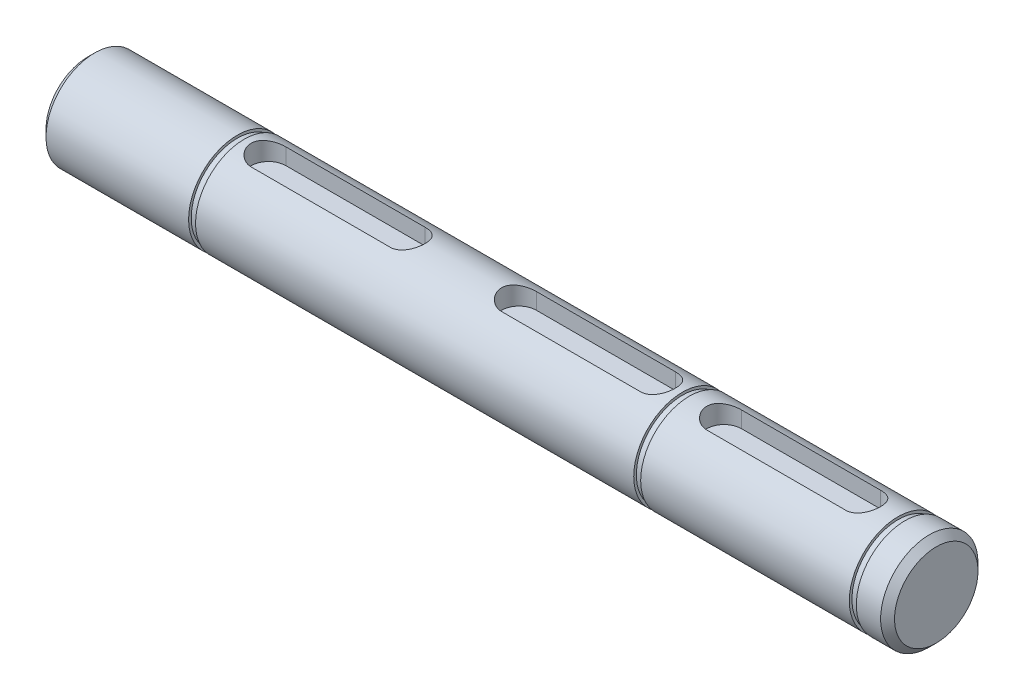
SolidWorks part; units mm, degrees
ref_plane "Front Plane" through (0, 0, 0) normal (0, 0, 1) x (1, 0, 0)
ref_plane "Top Plane" through (0, 0, 0) normal (0, 1, 0) x (1, 0, 0)
ref_plane "Right Plane" through (0, 0, 0) normal (1, 0, 0) x (0, 0, -1)
sketch "Sketch1" plane through (0, 0, 0) normal (1, 0, 0) x (0, 0, -1)
  circle A0 centre (0, 0) radius 7
  dimension "D1" = 14
extrude "Boss-Extrude1" add sketch "Sketch1" along normal mid plane 68
ref_plane "Plane1" through (0, 7, 0) normal (0, 1, 0) x (1, 0, 0)
sketch "Sketch4" plane through (0, 7, 0) normal (0, 1, 0) x (1, 0, 0)
  line L0 (-28, 0) -> (-8, 0) construction
  line L1 (-28, 2.5) -> (-8, 2.5)
  line L2 (-28, -2.5) -> (-8, -2.5)
  arc A0 (-28, 2.5) -> (-28, -2.5) centre (-28, 0) ccw
  arc A1 (-8, -2.5) -> (-8, 2.5) centre (-8, 0) ccw
  point P3 (-18, 0)
  dimension "D2" = 2.5
  dimension "D1" = 20
  dimension "D3" = 8
extrude "Cut-Extrude1" cut sketch "Sketch4" against normal blind 2.8
mirror "Mirror1" about plane through (0, 0, 0) normal (1, 0, 0) of "Cut-Extrude1"
sketch "Sketch5" plane through (-34, 0, 0) normal (-1, 0, 0) x (0, 0, 1)
  circle A1 centre (0, 0) radius 7
  circle A2 centre (0, 0) radius 7
  dimension "D1" = 0
extrude "Boss-Extrude3" add sketch "Sketch5" along normal blind 20
sketch "Sketch6" plane through (0, 0, 0) normal (0, 1, 0) x (1, 0, 0)
  line L0 (-54, 7) -> (-54, -7) construction
  line L1 (-46.5, 0) -> (-54, 0) construction
  circle A0 centre (-46.5, 0) radius 2.5
  dimension "D1" = 5
  dimension "D2" = 7.5
sketch "Sketch7" plane through (34, 0, 0) normal (1, 0, 0) x (0, 0, -1)
  circle A2 centre (0, 0) radius 7
  dimension "D1" = 14
extrude "Boss-Extrude4" add sketch "Sketch7" along normal blind 34
ref_plane "Plane2" through (0, 0, 7) normal (0, 0, 1) x (1, 0, 0)
sketch "Sketch11" plane through (0, 0, 0) normal (0, 0, 1) x (1, 0, 0)
  line L0 (68, 7) -> (30.5, 7) construction
  line L1 (63.5, 6.625) -> (62.5, 6.625)
  line L2 (63.5, 6.625) -> (63.5, 7.375)
  line L3 (63.5, 7.375) -> (62.5, 7.375)
  line L4 (62.5, 6.625) -> (62.5, 7.375)
  line L5 (63.5, 6.625) -> (62.5, 7.375) construction
  line L6 (63.5, 7.375) -> (62.5, 6.625) construction
  line L7 (68, 7) -> (30.5, 7) construction
  line L8 (32.5, 6.625) -> (31.5, 6.625)
  line L9 (32.5, 6.625) -> (32.5, 7.375)
  line L10 (32.5, 7.375) -> (31.5, 7.375)
  line L11 (31.5, 6.625) -> (31.5, 7.375)
  line L12 (32.5, 6.625) -> (31.5, 7.375) construction
  line L13 (32.5, 7.375) -> (31.5, 6.625) construction
  line L14 (68, -7) -> (68, 7) construction
  line L15 (-30.5, 7) -> (-54, 7) construction
  line L16 (-31.5, 6.625) -> (-32.5, 6.625)
  line L17 (-31.5, 6.625) -> (-31.5, 7.375)
  line L18 (-31.5, 7.375) -> (-32.5, 7.375)
  line L19 (-32.5, 6.625) -> (-32.5, 7.375)
  line L20 (-31.5, 6.625) -> (-32.5, 7.375) construction
  line L21 (-31.5, 7.375) -> (-32.5, 6.625) construction
  point P0 (63, 7)
  point P7 (32, 7)
  point P15 (-32, 7)
  dimension "D1" = 1
  dimension "D2" = 0.75
  dimension "D3" = 30
  dimension "D4" = 4.5
  dimension "D5" = 100
ref_axis "Axis1" through (71.5, 0, 0) along (-1, 0, 0)
revolve "Cut-Revolve1" cut sketch "Sketch11" angle 360 about axis through (71.5, 0, 0) along (-1, 0, 0)
chamfer "Chamfer1" distance 1 angle 45 2 edges at (-54, 0, 7) (68, 0, -7)
sketch "Sketch9" plane through (0, 7, 0) normal (0, 1, 0) x (1, 0, 0)
  line L0 (37.5, 0) -> (57.5, 0) construction
  line L1 (37.5, 2.5) -> (57.5, 2.5)
  line L2 (37.5, -2.5) -> (57.5, -2.5)
  line L3 (37.5, 0) -> (32.5, 0) construction
  line L5 (32.5, 7) -> (32.5, -7) construction
  line L6 (57.5, 0) -> (62.5, 0) construction
  line L7 (62.5, -6.625) -> (62.5, 6.625) construction
  arc A0 (37.5, 2.5) -> (37.5, -2.5) centre (37.5, 0) ccw
  arc A1 (57.5, -2.5) -> (57.5, 2.5) centre (57.5, 0) ccw
  point P3 (47.5, 0)
  dimension "D1" = 2.5
  dimension "D2" = 20
extrude "Cut-Extrude3" cut sketch "Sketch9" against normal blind 2.8
